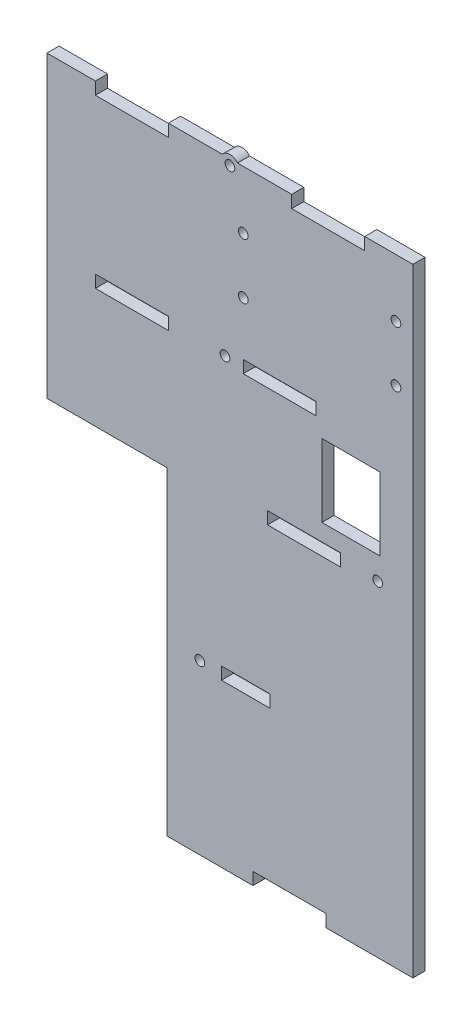
SolidWorks part; units mm, degrees
ref_plane "Front Plane" through (0, 0, 0) normal (0, 0, 1) x (1, 0, 0)
ref_plane "Top Plane" through (0, 0, 0) normal (0, 1, 0) x (1, 0, 0)
ref_plane "Right Plane" through (0, 0, 0) normal (1, 0, 0) x (0, 0, -1)
sketch "Sketch1" plane through (0, 0, 0) normal (0, 0, 1) x (1, 0, 0)
  line L1 (-75.5, 127.5) -> (75.5, 127.5)
  line L2 (-75.5, 127.5) -> (-75.5, -127.5)
  line L3 (-75.5, -127.5) -> (75.5, -127.5)
  line L4 (75.5, 127.5) -> (75.5, -127.5)
  dimension "D1" = 151
  dimension "D2" = 255
  dimension "D3" = 75.5
  dimension "D4" = 127.5
extrude "Boss-Extrude1" add sketch "Sketch1" along normal blind 5
sketch "Sketch2" plane through (0, 0, 5) normal (0, 0, 1) x (1, 0, 0)
  line L0 (-75.5, 4.0829) -> (-26.0135, 4.0829)
  line L1 (-75.5, 4.0829) -> (-75.5, -127.5)
  line L2 (-75.5, -127.5) -> (-26.0135, -127.5)
  line L3 (-26.0135, 4.0829) -> (-26.0135, -127.5)
  line L4 (-75.5, -127.5) -> (75.5, -127.5) construction
  line L7 (-75.5, 127.5) -> (-75.5, -127.5) construction
  dimension "D1" = 49.4865
extrude "Cut-Extrude1" cut sketch "Sketch2" against normal blind 5
sketch "Sketch3" plane through (0, 0, 5) normal (0, 0, 1) x (1, 0, 0)
  line L0 (-40.45, 127.5) -> (-40.45, 122.4) construction
  line L1 (40.55, 127.5) -> (40.55, 122.4) construction
  line L2 (-40.4402, 58.5) -> (-40.4402, 53.4) construction
  line L3 (20.55, 58.5) -> (20.55, 53.4) construction
  line L4 (30.55, 9.5) -> (30.55, 4.4) construction
  line L5 (6.55, -55.5) -> (6.55, -60.6) construction
  line L6 (24.55, -122.4) -> (24.55, -127.5) construction
  line L7 (-55.5, 124.95) -> (-25.4, 124.95) construction
  line L8 (-25.4, 127.5) -> (-55.5, 127.5)
  line L9 (-55.5, 127.5) -> (-55.5, 122.4)
  line L10 (-55.5, 122.4) -> (-25.4, 122.4)
  line L11 (-25.4, 122.4) -> (-25.4, 127.5)
  line L12 (25.5, 124.95) -> (55.6, 124.95) construction
  line L13 (-55.4902, 55.95) -> (-25.3902, 55.95) construction
  line L14 (5.5, 55.95) -> (35.6, 55.95) construction
  line L15 (15.5, 6.95) -> (45.6, 6.95) construction
  line L16 (55.6, 127.5) -> (25.5, 127.5)
  line L17 (25.5, 127.5) -> (25.5, 122.4)
  line L18 (25.5, 122.4) -> (55.6, 122.4)
  line L19 (55.6, 122.4) -> (55.6, 127.5)
  line L20 (-3.5, -58.05) -> (16.6, -58.05) construction
  line L21 (9.5, -124.95) -> (39.6, -124.95) construction
  line L22 (75.5, 127.5) -> (-75.5, 127.5) construction
  line L24 (-25.3902, 58.5) -> (-55.4902, 58.5)
  line L25 (-55.4902, 58.5) -> (-55.4902, 53.4)
  line L26 (-55.4902, 53.4) -> (-25.3902, 53.4)
  line L27 (-25.3902, 53.4) -> (-25.3902, 58.5)
  line L28 (-55.5, 58.5) -> (-25.5, 58.5) construction
  line L29 (15.5, 9.5) -> (45.5, 9.5) construction
  line L30 (-3.5, -55.5) -> (16.5, -55.5) construction
  line L32 (35.6, 58.5) -> (5.5, 58.5)
  line L33 (5.5, 58.5) -> (5.5, 53.4)
  line L34 (5.5, 53.4) -> (35.6, 53.4)
  line L35 (35.6, 53.4) -> (35.6, 58.5)
  line L40 (45.6, 9.5) -> (15.5, 9.5)
  line L41 (15.5, 9.5) -> (15.5, 4.4)
  line L42 (15.5, 4.4) -> (45.6, 4.4)
  line L43 (45.6, 4.4) -> (45.6, 9.5)
  line L48 (16.6, -55.5) -> (-3.5, -55.5)
  line L49 (-3.5, -55.5) -> (-3.5, -60.6)
  line L50 (-3.5, -60.6) -> (16.6, -60.6)
  line L51 (16.6, -60.6) -> (16.6, -55.5)
  line L56 (39.6, -122.4) -> (9.5, -122.4)
  line L57 (9.5, -122.4) -> (9.5, -127.5)
  line L58 (9.5, -127.5) -> (39.6, -127.5)
  line L59 (39.6, -127.5) -> (39.6, -122.4)
  dimension "D1" = 15.05
  dimension "D2" = 15.05
  dimension "D3" = 15.05
  dimension "D4" = 15.05
  dimension "D5" = 15.05
  dimension "D6" = 10.05
  dimension "D7" = 15.05
  dimension "D8" = 2.55
  dimension "D9" = 5.1
  dimension "D10" = 2.55
  dimension "D11" = 5.1
  dimension "D12" = 5.1
  dimension "D13" = 5.1
  dimension "D14" = 5.1
extrude "Cut-Extrude2" cut sketch "Sketch3" against normal blind 5
sketch "Sketch4" plane through (0, 0, 5) normal (0, 0, 1) x (1, 0, 0)
  circle A0 centre (0, 125) radius 2
  circle A1 centre (-2.045, 56) radius 2
  circle A2 centre (60.9367, 7) radius 2
  circle A3 centre (-12.4056, -58) radius 2
  dimension "D1" = 4
  dimension "D2" = 4
  dimension "D3" = 4
  dimension "D4" = 4
extrude "Cut-Extrude3" cut sketch "Sketch4" against normal up to vertex (5 mm away)
sketch "Sketch5" plane through (0, 0, 5) normal (0, 0, 1) x (1, 0, 0)
  circle A0 centre (0, 125) radius 2
  circle A1 centre (0, 125) radius 4
  dimension "D1" = 8
extrude "Boss-Extrude2" add sketch "Sketch5" against normal blind 5
sketch "Sketch6" plane through (0, 0, 5) normal (0, 0, 1) x (1, 0, 0)
  line L4 (61.942, 16.5) -> (61.942, 46.5)
  line L5 (37.942, 16.5) -> (61.942, 16.5)
  line L6 (37.942, 46.5) -> (37.942, 16.5)
  line L7 (61.942, 46.5) -> (37.942, 46.5)
extrude "Cut-Extrude4" cut sketch "Sketch6" against normal blind 5
sketch "Sketch7" plane through (0, 0, 5) normal (0, 0, 1) x (1, 0, 0)
  circle A1 centre (68.5, 103.5803) radius 2
  circle A5 centre (5.5, 80.5803) radius 2
  circle A6 centre (5.5, 103.5803) radius 2
  circle A7 centre (68.5, 80.5803) radius 2
  dimension "D1" = 4
  dimension "D2" = 4
  dimension "D3" = 4
  dimension "D4" = 4
extrude "Cut-Extrude5" cut sketch "Sketch7" against normal blind 10
